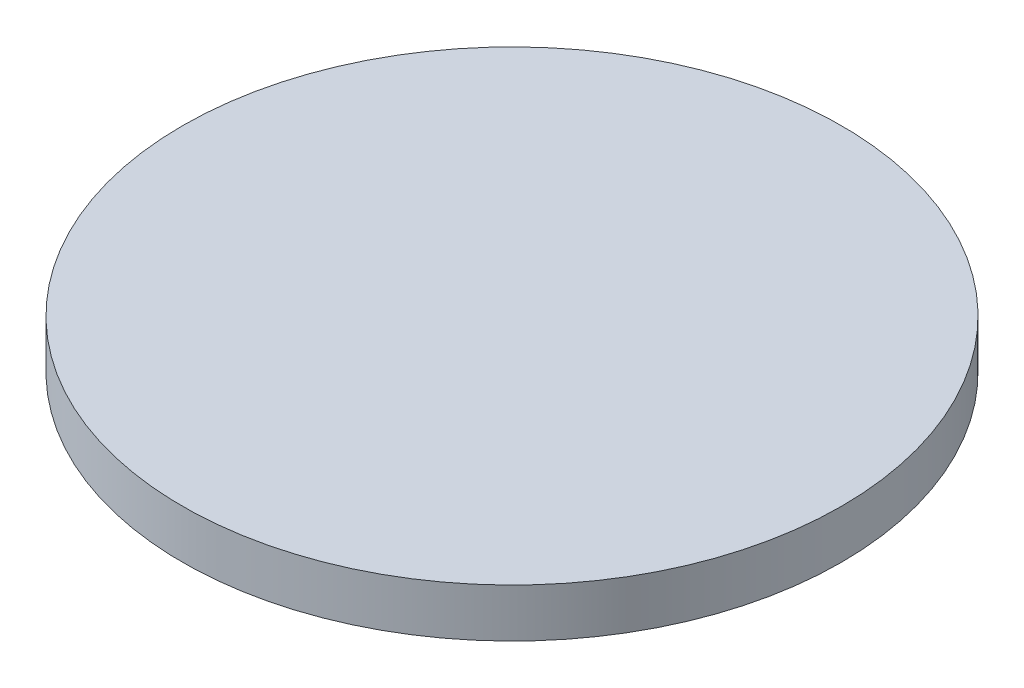
SolidWorks part; units mm, degrees
material "Glass"
ref_plane "Front Plane" through (0, 0, 0) normal (0, 0, 1) x (1, 0, 0)
ref_plane "Top Plane" through (0, 0, 0) normal (0, 1, 0) x (1, 0, 0)
ref_plane "Right Plane" through (0, 0, 0) normal (1, 0, 0) x (0, 0, -1)
sketch "Sketch1" plane through (0, 0, 0) normal (0, 0, 1) x (1, 0, 0)
  line L0 (-55.2, -0.2) -> (-52.5, -0.2)
  line L1 (0, 0) -> (-55, 0)
  line L2 (0, 0) -> (0, 8.1)
  line L3 (0, 8.1) -> (-55, 8.1)
  line L4 (-55, 0) -> (-55, 8.1)
  line L5 (-52.5, -0.2) -> (-52.5, -3.2)
  line L6 (-52.5, -3.2) -> (-63.2, -3.2)
  line L7 (-63.2, -3.2) -> (-63.2, 11.8)
  line L12 (-55.2, 11.8) -> (-55.2, -0.2)
  line L13 (-55.2, 11.8) -> (-63.2, 11.8)
  line L14 (0, 0) -> (0, 30.013) construction
sketch "Sketch3" plane through (0, 0, 0) normal (0, 0, 1) x (1, 0, 0)
  line L0 (0, 0) -> (0, 30.013) construction
  line L1 (0, 0) -> (0, 8.1) construction
  line L2 (0, 0) -> (-55, 0) construction
  line L3 (-55, 0) -> (-55, 8.1) construction
  line L4 (0, 8.1) -> (-55, 8.1) construction
  line L5 (0, 0) -> (0, 30.013) construction
  line L6 (0, 0) -> (0, 8.1)
  line L7 (0, 0) -> (-55, 0)
  line L8 (-55, 0) -> (-55, 8.1)
  line L9 (0, 8.1) -> (-55, 8.1)
revolve "Filter" add sketch "Sketch3" angle 360 about L5
